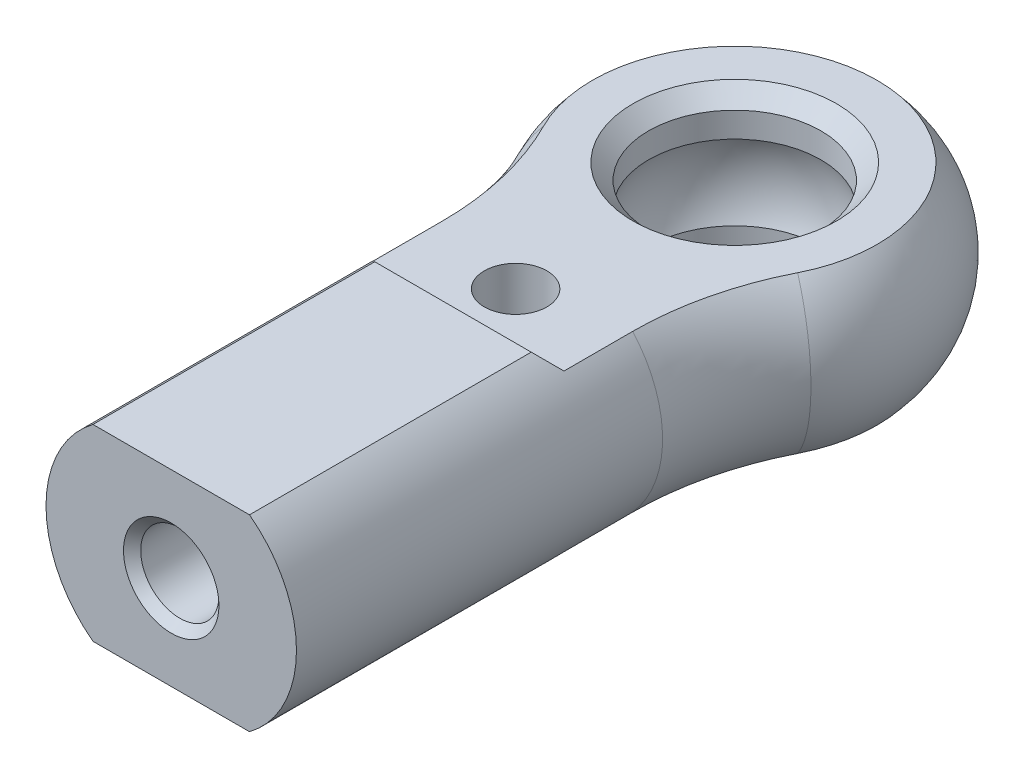
SolidWorks part; units mm, degrees
material "Nylon 101"
ref_plane "Front Plane" through (0, 0, 0) normal (0, 0, 1) x (1, 0, 0)
ref_plane "Top Plane" through (0, 0, 0) normal (0, 1, 0) x (1, 0, 0)
ref_plane "Right Plane" through (0, 0, 0) normal (1, 0, 0) x (0, 0, -1)
sketch "Sketch1" plane through (0, 0, 0) normal (0, 1, 0) x (1, 0, 0)
  line L2 (-2.5, -3.1225) -> (-2.5, -18)
  line L3 (-2.5, -18) -> (2.5, -18)
  line L4 (2.5, -3.1225) -> (2.5, -18)
  arc A0 (2.5, -3.1225) -> (-2.5, -3.1225) centre (0, 0) ccw
  point P1 (0, -18)
  dimension "D1" = 4
  dimension "D2" = 18
  dimension "D3" = 5
extrude "Boss-Extrude1" add sketch "Sketch1" along normal mid plane 6
fillet "Fillet1" radius 10 2 edges at (-2.5, 0, 3.1225) (2.5, 0, 3.1225)
sketch "Sketch2" plane through (0, 0, 18) normal (0, 0, 1) x (1, 0, 0)
  line L2 (2.5, 3) -> (2.5, -3)
  arc A0 (2.5, 3) -> (2.5, -3) centre (0.25, 0) cw
  point P9 (0, 0)
  dimension "D1" = 4
sketch "Sketch3" plane through (0, 3, 0) normal (0, 1, 0) x (1, 0, 0)
  line L0 (2.5, -18) -> (2.5, -6.3048) construction
  line L1 (-2.5, -6.3048) -> (-2.5, -18) construction
  line L2 (2.5, -18) -> (2.5, -6.3048)
  line L3 (-2.5, -6.3048) -> (-2.5, -18)
  arc A0 (3.5714, -1.8014) -> (2.5, -6.3048) centre (12.5, -6.3048) ccw construction
  arc A1 (3.5714, -1.8014) -> (-3.5714, -1.8014) centre (0, 0) ccw construction
  arc A2 (-2.5, -6.3048) -> (-3.5714, -1.8014) centre (-12.5, -6.3048) ccw construction
  arc A3 (3.5714, -1.8014) -> (2.5, -6.3048) centre (12.5, -6.3048) ccw
  arc A4 (3.5714, -1.8014) -> (-3.5714, -1.8014) centre (0, 0) ccw
  arc A5 (-2.5, -6.3048) -> (-3.5714, -1.8014) centre (-12.5, -6.3048) ccw
sweep "Sweep1" add profiles "Sketch2" path "Sketch3"
hole_wizard "M3 Tapped Hole1" positions "Sketch5" profile "Sketch4" tap size "M3" standard "DIN"
sketch "Sketch5" plane through (0, 0, 18) normal (0, 0, 1) x (1, 0, 0)
  point P0 (0, 0)
sketch "Sketch4" plane through (0, 0, 18) normal (1, 0, 0) x (0, -1, 0)
  line L0 (0, 0) -> (0, 5.7511)
  line L1 (0, 5.7511) -> (1.25, 5)
  line L2 (1.25, 5) -> (1.25, 0.275)
  line L3 (1.25, 0.275) -> (1.525, 0)
  line L5 (1.525, 0) -> (0, 0)
  line L6 (-1.25, 0.275) -> (-1.525, 0) construction
  line L10 (0, 5.7511) -> (-1.25, 5) construction
  line L11 (0, -6.35) -> (0, 107.95) construction
  dimension "Tap Drill Dia." = 2.5
  dimension "Tap Drill Depth" = 5
  dimension "Near C'Sink Dia." = 3.05
  dimension "Near C'Sink Angle" = 90
  dimension "Drill Angle" = 118
cosmetic thread "Hole Thread1" parameters "D1"=5, "D2"=3
sketch "Sketch6" plane through (0, 0, 0) normal (1, 0, 0) x (0, 0, -1)
  line L0 (-9, 3) -> (-8.5, 2.5)
  line L1 (-8.5, 2.5) -> (11, 2.5)
  line L2 (11, 2.5) -> (11, 3)
  line L3 (11, 3) -> (-9, 3)
  line L4 (-6.3048, 3) -> (-18, 3) construction
  dimension "D1" = 2.5
  dimension "D2" = 9
  dimension "D3" = 45
  dimension "D4" = 20
extrude "Cut-Extrude1" cut sketch "Sketch6" against normal through all and the other way through all
mirror "Mirror1" about plane through (0, 0, 0) normal (0, 1, 0) of "Cut-Extrude1"
sketch "Sketch7" plane through (0, 0, 0) normal (1, 0, 0) x (0, 0, -1)
  line L0 (0, 6.2776) -> (0, -6.7385) construction
  line L1 (0, 3) -> (0, -3)
  line L2 (0, 3) -> (2.75, 3)
  line L3 (2.75, 3) -> (2.75, 1.199)
  line L4 (2.75, -3) -> (0, -3)
  line L5 (2.75, -1.199) -> (2.75, -3)
  arc A0 (2.75, 1.199) -> (2.75, -1.199) centre (0, 0) cw
  dimension "D1" = 3
  dimension "D2" = 5.5
revolve "Cut-Revolve1" cut sketch "Sketch7" angle 360 about L0
sketch "Sketch8" plane through (0, 0, 0) normal (0, 1, 0) x (1, 0, 0)
  circle A0 centre (0, -7) radius 1
  dimension "D1" = 2
  dimension "D2" = 7
extrude "Cut-Extrude2" cut sketch "Sketch8" against normal through all and the other way through all
chamfer "Chamfer1" distance 0.5 angle 45 2 edges at (0, -2.5, -2.75) (0, 2.5, -2.75)
